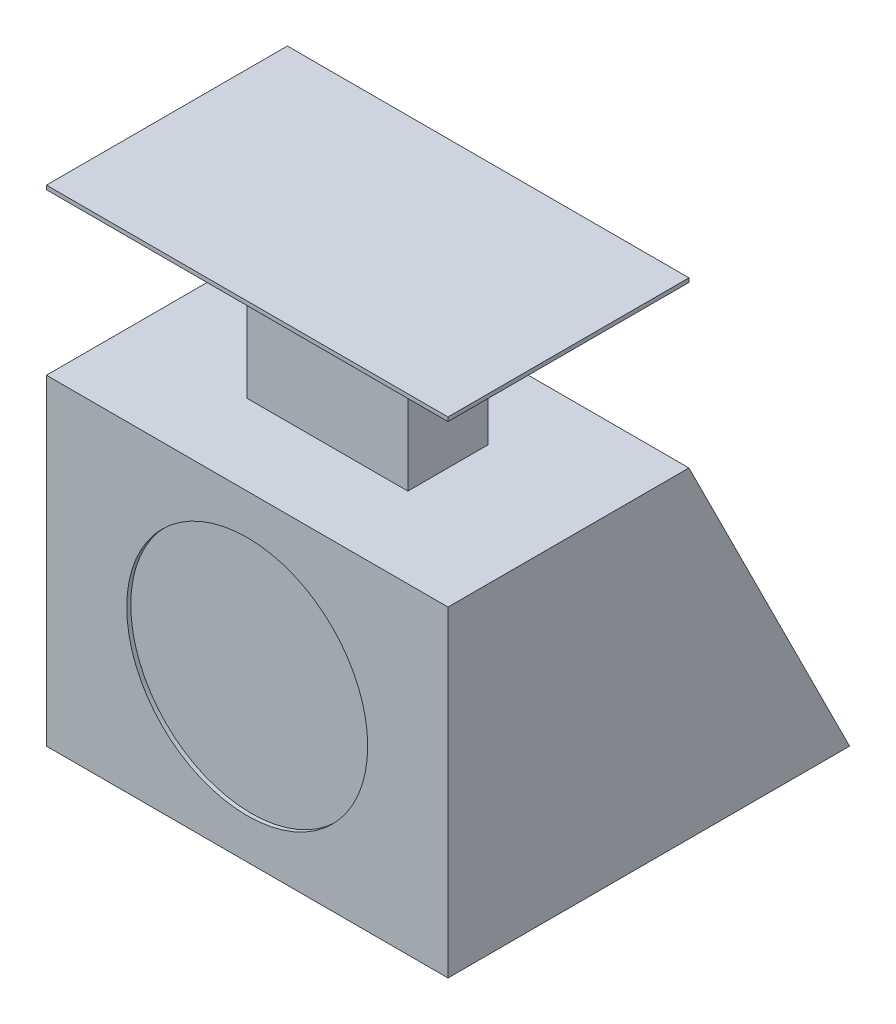
SolidWorks part; units mm, degrees
ref_plane "Front" through (0, 0, 0) normal (0, 0, 1) x (1, 0, 0)
ref_plane "Top" through (0, 0, 0) normal (0, 1, 0) x (1, 0, 0)
ref_plane "Right" through (0, 0, 0) normal (1, 0, 0) x (0, 0, -1)
sketch "Sketch1" plane through (0, 0, 0) normal (1, 0, 0) x (0, 0, -1)
  line L0 (100, 0) -> (0, 0)
  line L1 (0, 0) -> (0, 80)
  line L2 (0, 80) -> (60, 80)
  line L3 (60, 80) -> (100, 0)
  dimension "D1" = 100
  dimension "D2" = 80
  dimension "D3" = 60
extrude "Extrude1" add sketch "Sketch1" along normal blind 100
sketch "Sketch2" plane through (0, 0, 0) normal (0, 0, 1) x (1, 0, 0)
  circle A0 centre (50, 40) radius 30
extrude "Cut-Extrude1" cut sketch "Sketch2" against normal blind 1
sketch "Sketch3" plane through (0, 80, 0) normal (0, 1, 0) x (-1, 0, 0)
  line L0 (-30, -20) -> (-70, -20)
  line L5 (-30, -40) -> (-70, -40)
  line L6 (-30, -20) -> (-30, -40)
  line L7 (-70, -20) -> (-70, -40)
extrude "Extrude2" add sketch "Sketch3" along normal blind 40
sketch "Sketch4" plane through (0, 120, 0) normal (0, 1, 0) x (-1, 0, 0)
  line L1 (-100, 0) -> (0, 0)
  line L2 (-100, 0) -> (-100, -60)
  line L3 (-100, -60) -> (0, -60)
  line L4 (0, 0) -> (0, -60)
extrude "Extrude3" add sketch "Sketch4" along normal blind 1
